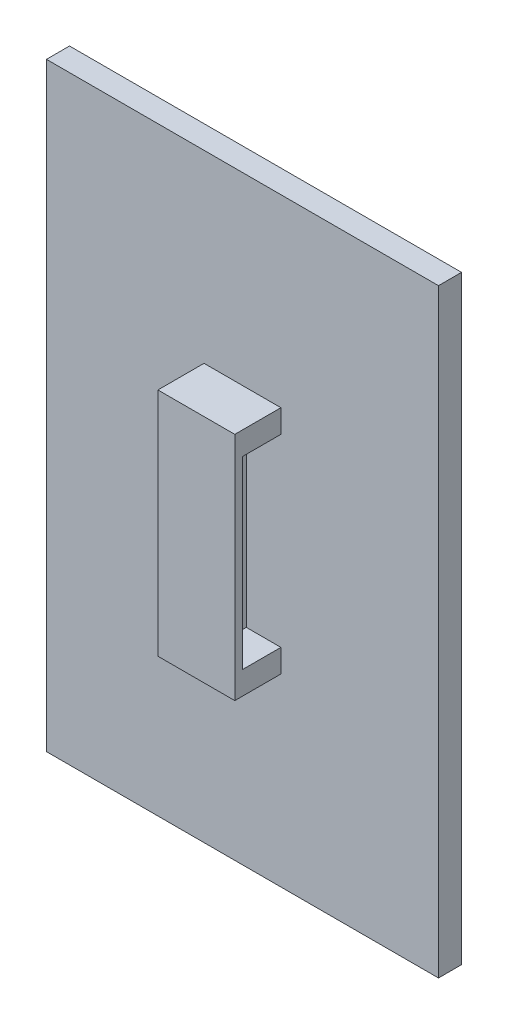
SolidWorks part; units mm, degrees
ref_plane "Front Plane" through (0, 0, 0) normal (0, 0, 1) x (1, 0, 0)
ref_plane "Top Plane" through (0, 0, 0) normal (0, 1, 0) x (1, 0, 0)
ref_plane "Right Plane" through (0, 0, 0) normal (1, 0, 0) x (0, 0, -1)
sketch "Sketch1" plane through (0, 0, 0) normal (0, 0, 1) x (1, 0, 0)
  line L1 (0, 0) -> (-51, 0)
  line L2 (0, 0) -> (0, 78)
  line L3 (0, 78) -> (-51, 78)
  line L4 (-51, 0) -> (-51, 78)
  dimension "D1" = 51
  dimension "D2" = 78
extrude "Boss-Extrude1" add sketch "Sketch1" along normal blind 3
sketch "Sketch2" plane through (0, 0, 3) normal (0, 0, 1) x (1, 0, 0)
  line L1 (-20.5, 54) -> (-30.5, 54)
  line L2 (-20.5, 54) -> (-20.5, 24)
  line L3 (-20.5, 24) -> (-30.5, 24)
  line L4 (-30.5, 54) -> (-30.5, 24)
  line L5 (0, 0) -> (0, 78) construction
  line L6 (-51, 0) -> (0, 0) construction
  point P4 (0, 39)
  point P5 (-20.5, 39)
  point P8 (-25.5, 24)
  point P10 (-25.5, 0)
  dimension "D1" = 10
  dimension "D2" = 30
extrude "Boss-Extrude3" add sketch "Sketch2" along normal blind 6
sketch "Sketch3" plane through (-30.5, 0, 0) normal (-1, 0, 0) x (0, 0, 1)
  line L0 (3, 54) -> (3, 24) construction
  line L1 (3, 51) -> (9, 51)
  line L2 (3, 51) -> (3, 27)
  line L3 (3, 27) -> (9, 27)
  line L4 (9, 51) -> (9, 27)
  line L5 (9, 24) -> (3, 24) construction
  line L6 (9, 54) -> (3, 54) construction
  line L7 (9, 54) -> (9, 24) construction
  dimension "D1" = 3
  dimension "D2" = 3
  dimension "D3" = 0
extrude "Cut-Extrude1" cut sketch "Sketch3" against normal through all
sketch "Sketch5" plane through (0, 51, 0) normal (0, -1, 0) x (1, 0, 0)
  line L0 (-30.5, 9) -> (-20.5, 9)
  line L1 (-20.5, 9) -> (-20.5, 8)
  line L2 (-20.5, 9) -> (-20.5, 3) construction
  line L3 (-20.5, 8) -> (-25, 4)
  line L4 (-20.5, 3) -> (-30.5, 3) construction
  line L5 (-26, 4) -> (-30.5, 8)
  line L6 (-30.5, 9) -> (-30.5, 3) construction
  line L7 (-30.5, 8) -> (-30.5, 9)
  line L8 (-26, 4) -> (-26, 3)
  line L9 (-26, 3) -> (-25, 3)
  line L10 (-25, 3) -> (-25, 4)
  point P4 (-25.5, 3)
  point P13 (-25.5, 3)
  point P18 (0, 0)
  dimension "D1" = 1
  dimension "D2" = 1
  dimension "D3" = 1
  dimension "D4" = 1
  dimension "D5" = 1
extrude "Boss-Extrude4" add sketch "Sketch5" along normal up to next
